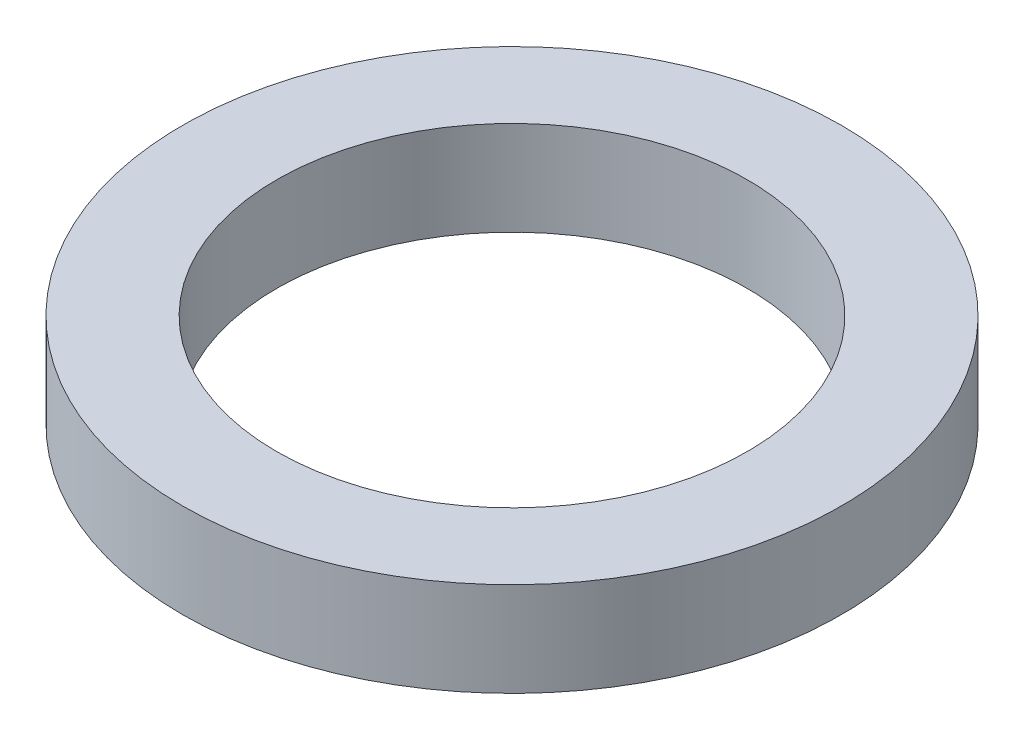
SolidWorks part; units mm, degrees
ref_plane "Alzado" through (0, 0, 0) normal (0, 0, 1) x (1, 0, 0)
ref_plane "Planta" through (0, 0, 0) normal (0, 1, 0) x (1, 0, 0)
ref_plane "Vista lateral" through (0, 0, 0) normal (1, 0, 0) x (0, 0, -1)
sketch "Croquis1" plane through (0, 0, 0) normal (0, 1, 0) x (1, 0, 0)
  line L0 (0, 0) -> (0, 49.2428) construction
  circle A0 centre (0, 0) radius 5 construction
  circle A1 centre (0, 15) radius 10 construction
  circle A2 centre (0, 0) radius 25
  circle A3 centre (0, 0) radius 35
  dimension "D1" = 10
  dimension "D2" = 50
  dimension "D3" = 10
extrude "Saliente-Extruir1" add sketch "Croquis1" along normal blind 10
